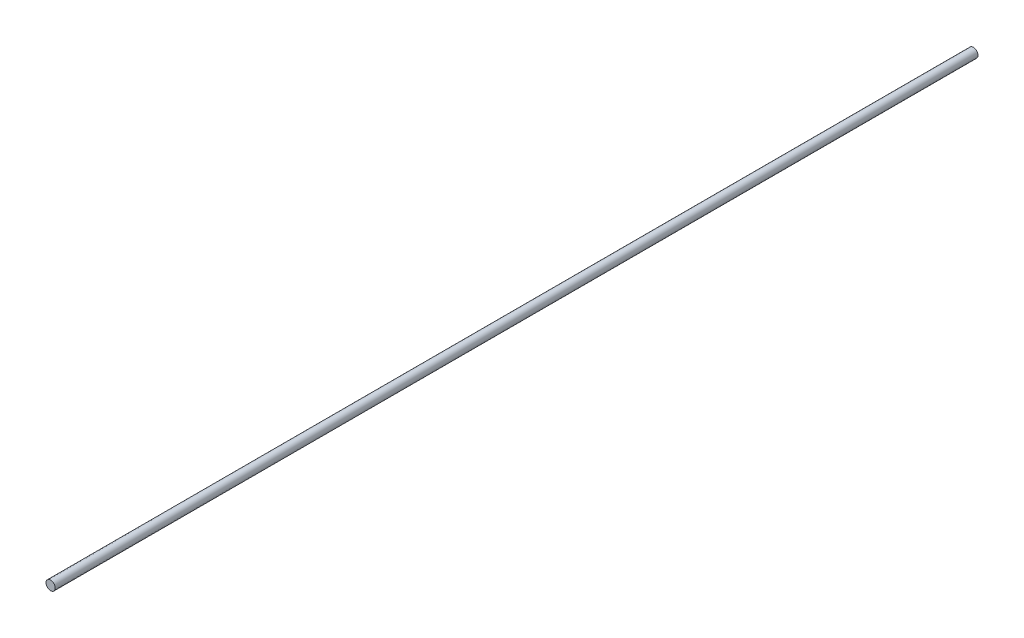
SolidWorks part; units mm, degrees
material "AISI 1020 Steel, Cold Rolled"
ref_plane "Front Plane" through (0, 0, 0) normal (0, 0, 1) x (1, 0, 0)
ref_plane "Top Plane" through (0, 0, 0) normal (0, 1, 0) x (1, 0, 0)
ref_plane "Right Plane" through (0, 0, 0) normal (1, 0, 0) x (0, 0, -1)
sketch "Sketch1" plane through (0, 0, 0) normal (0, 0, 1) x (1, 0, 0)
  circle A0 centre (0, 0) radius 4
  dimension "D1" = 8
extrude "Boss-Extrude1" add sketch "Sketch1" along normal mid plane 800
cosmetic thread "Cosmetic Thread3" parameters "D2"=6.619
